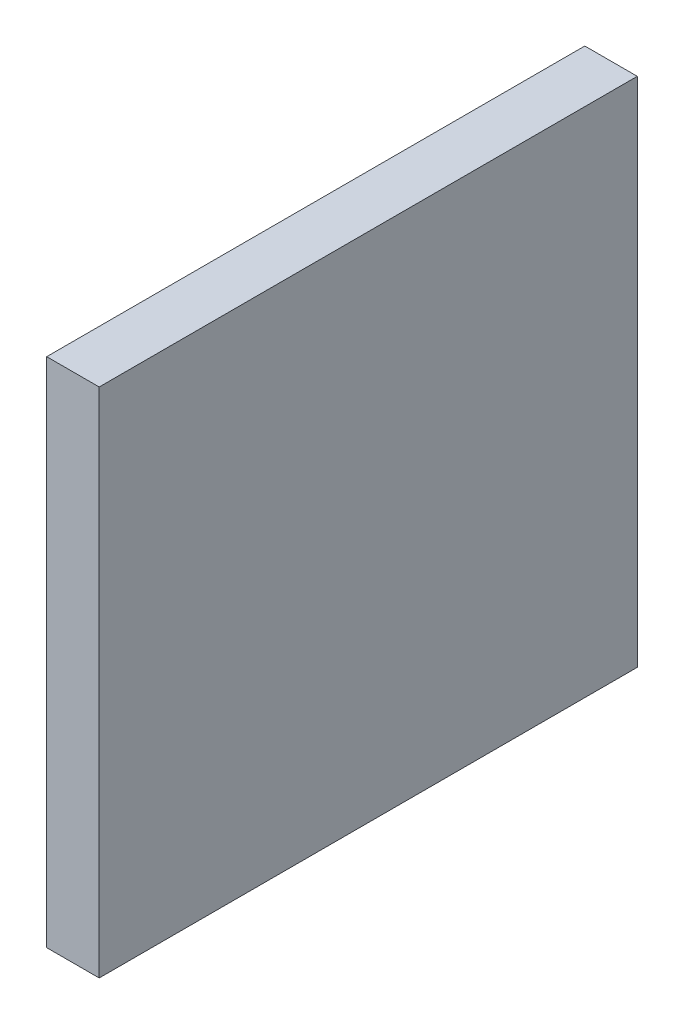
SolidWorks part; units mm, degrees
ref_plane "Front Plane" through (0, 0, 0) normal (0, 0, 1) x (1, 0, 0)
ref_plane "Top Plane" through (0, 0, 0) normal (0, 1, 0) x (1, 0, 0)
ref_plane "Right Plane" through (0, 0, 0) normal (1, 0, 0) x (0, 0, -1)
sketch "Sketch3" plane through (0, 0, 0) normal (1, 0, 0) x (0, 0, -1)
  line L0 (0, 0) -> (0, 39)
  line L1 (0, 39) -> (41, 39)
  line L2 (41, 39) -> (41, 0)
  line L3 (41, 0) -> (0, 0)
  dimension "D1" = 41
  dimension "D2" = 39
extrude "Boss-Extrude2" add sketch "Sketch3" along normal blind 4 contours L3 L0 L1 L2
